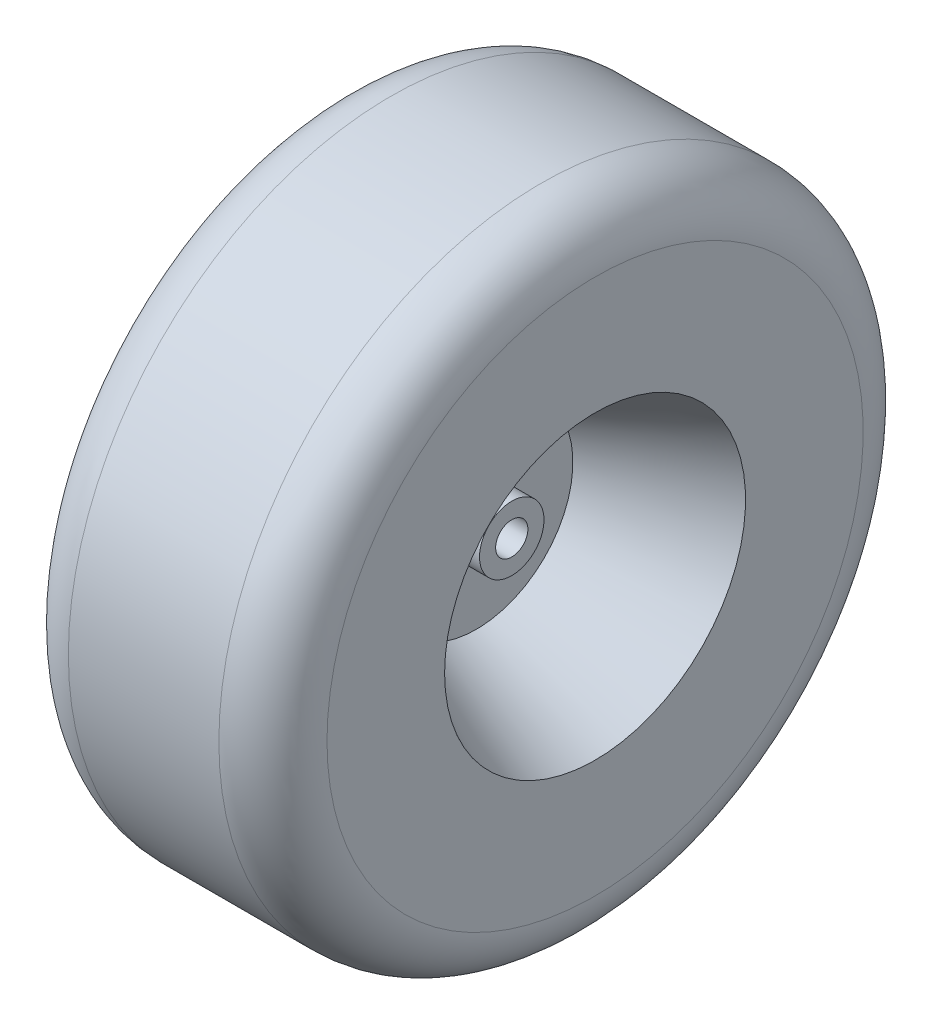
SolidWorks part; units mm, degrees
ref_plane "Front Plane" through (0, 0, 0) normal (0, 0, 1) x (1, 0, 0)
ref_plane "Top Plane" through (0, 0, 0) normal (0, 1, 0) x (1, 0, 0)
ref_plane "Right Plane" through (0, 0, 0) normal (1, 0, 0) x (0, 0, -1)
sketch "Sketch1" plane through (0, 0, 0) normal (0, 0, 1) x (1, 0, 0)
  line L0 (0, 0) -> (0, 190.5) construction
  line L1 (-76.2, 190.5) -> (76.2, 190.5) construction
  line L2 (76.2, 190.5) -> (76.2, 88.9) construction
  line L3 (-76.2, 0) -> (76.2, 0) construction
  line L4 (0, 0) -> (0, 9.525) construction
  line L5 (-26.9875, 9.525) -> (26.9875, 9.525)
  line L6 (76.2, 88.9) -> (76.2, 0) construction
  line L7 (26.9875, 9.525) -> (26.9875, 19.05)
  line L8 (26.9875, 19.05) -> (6.1126, 19.05)
  line L9 (6.1126, 19.05) -> (6.1126, 56.9746)
  line L10 (6.1126, 56.9746) -> (76.2, 88.9)
  line L11 (-44.45, 190.5) -> (44.45, 190.5)
  line L12 (76.2, 88.9) -> (76.2, 158.373)
  line L13 (-76.2, 88.9) -> (-76.2, 0) construction
  line L14 (-76.2, 190.5) -> (-76.2, 88.9) construction
  line L15 (-76.2, 88.9) -> (-76.2, 158.373)
  line L16 (-6.1126, 56.9746) -> (-76.2, 88.9)
  line L17 (-6.1126, 19.05) -> (-6.1126, 56.9746)
  line L18 (-26.9875, 19.05) -> (-6.1126, 19.05)
  line L19 (-26.9875, 9.525) -> (-26.9875, 19.05)
  arc A0 (44.45, 190.5) -> (76.2, 158.373) centre (44.073, 158.3752) cw
  arc A1 (-44.45, 190.5) -> (-76.2, 158.373) centre (-44.073, 158.3752) ccw
  point P11 (0, 9.525)
  dimension "D1" = 190.5
  dimension "D2" = 76.2
  dimension "D3" = 101.6
  dimension "D4" = 9.525
  dimension "D5" = 49.2125
  dimension "D6" = 9.525
  dimension "D7" = 44.45
revolve "Revolve1" add sketch "Sketch1" angle 360 about L3
sketch "Sketch2" plane through (0, 0, 0) normal (1, 0, 0) x (0, 0, -1)
  line L0 (0, 0) -> (0, -190.5) construction
  line L1 (0, 0) -> (0, 190.5)
  circle A0 centre (0, 0) radius 190.5
